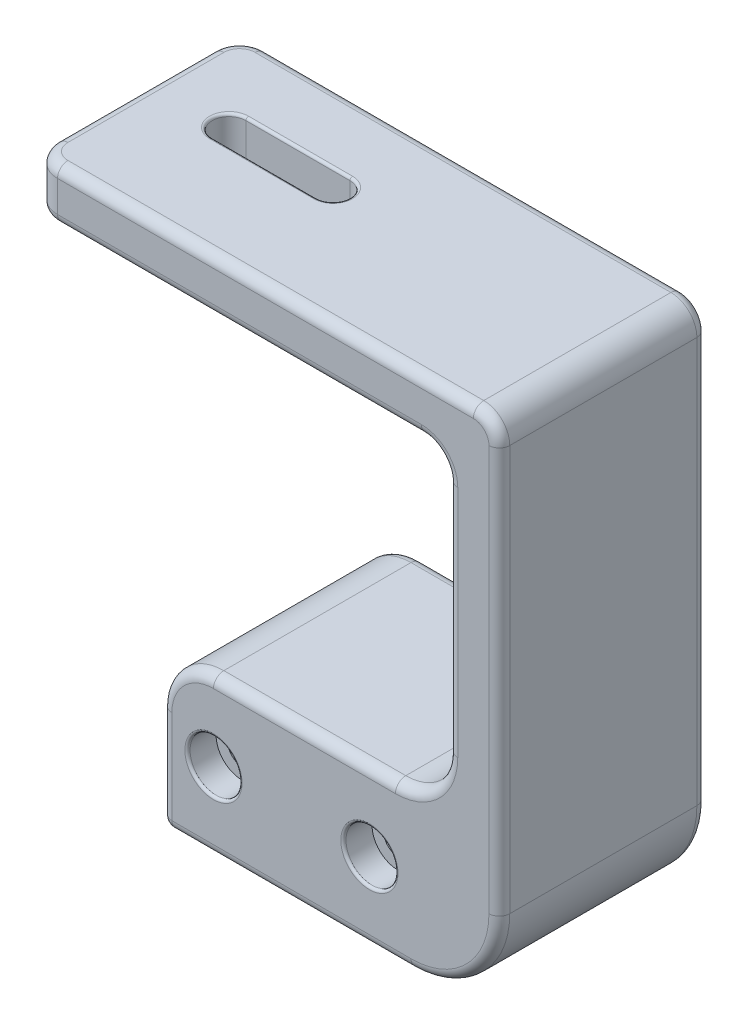
SolidWorks part; units mm, degrees
material "ABS"
ref_plane "Ebene vorne" through (0, 0, 0) normal (0, 0, 1) x (1, 0, 0)
ref_plane "Ebene oben" through (0, 0, 0) normal (0, 1, 0) x (1, 0, 0)
ref_plane "Ebene rechts" through (0, 0, 0) normal (1, 0, 0) x (0, 0, -1)
sketch "Skizze1" plane through (0, 0, 0) normal (0, 0, 1) x (1, 0, 0)
  line L0 (-50, 100) -> (-50, 90)
  line L1 (22, 0) -> (-22, 0) construction
  line L2 (30, 30) -> (-25, 30)
  line L3 (-50, 100) -> (40, 100)
  line L4 (40, 100) -> (40, 0)
  line L5 (40, 0) -> (-25, 0)
  line L6 (-50, 90) -> (30, 90)
  line L7 (-25, 0) -> (-25, 30)
  line L8 (0, -22) -> (0, 22) construction
  line L9 (30, 90) -> (30, 30)
  dimension "D2" = 55
  dimension "D1" = 25
  dimension "D3" = 10
  dimension "D5" = 100
  dimension "D4" = 65
  dimension "D6" = 30
  dimension "D7" = 90
extrude "Aufsatz-Linear austragen1" add sketch "Skizze1" along normal mid plane 40
sketch "Skizze3" plane through (0, 100, 0) normal (0, 1, 0) x (1, 0, 0)
  line L0 (-35, 3) -> (-15, 3) construction
  line L1 (-35, 6.25) -> (-15, 6.25)
  line L2 (-35, -0.25) -> (-15, -0.25)
  line L3 (-50, -20) -> (-50, 20) construction
  line L5 (40, 20) -> (-50, 20) construction
  arc A0 (-35, 6.25) -> (-35, -0.25) centre (-35, 3) ccw
  arc A1 (-15, -0.25) -> (-15, 6.25) centre (-15, 3) ccw
  point P3 (-25, 3)
  dimension "D1" = 6.5
  dimension "D2" = 20
  dimension "D3" = 15
  dimension "D4" = 17
extrude "Schnitt-Linear austragen1" cut sketch "Skizze3" against normal blind 20
sketch "Skizze5" plane through (0, 0, 20) normal (0, 0, 1) x (1, 0, 0)
  line L2 (0, -22) -> (0, 22) construction
  line L3 (-25, 0) -> (40, 0) construction
  point P0 (-15, 15)
  point P1 (15, 15)
  point P6 (3.3182, -18.595)
  point P7 (2.4434, -16.9467)
  dimension "D1" = 15
  dimension "D2" = 30
  dimension "D3" = 15
sketch "Skizze7" plane through (0, 0, 0) normal (0, -1, 0) x (1, 0, 0)
  line L0 (0, -22) -> (0, 22) construction
  line L1 (49.5, 0) -> (-49.5, 0) construction
  circle A0 centre (0, 10) radius 4
  circle A1 centre (0, -10) radius 4
  dimension "D1" = 8
  dimension "D2" = 20
  dimension "D3" = 10
extrude "Schnitt-Linear austragen3" cut sketch "Skizze7" against normal blind 12
hole_wizard "Stirnsenkung fur M3 Senkschraube (Kopf Button)1" positions "3D-Skizze1" profile "Skizze8" counterbore size "M3" standard "Ansi Metrisch" end condition through all
sketch3d "3D-Skizze1"
  point P0 (-15, 15, 20)
  point P3 (15, 15, 20)
sketch "Skizze8" plane through (-15, 15, 20) normal (1, 0, 0) x (0, -1, 0)
  line L0 (0, 0) -> (0, 40)
  line L1 (0, 40) -> (2.75, 40)
  line L3 (2.75, 40) -> (2.75, 5.5)
  line L4 (2.75, 5.5) -> (5, 5.5)
  line L5 (5, 5.5) -> (5, 0)
  line L7 (5, 0) -> (0, 0)
  line L11 (0, -6.35) -> (0, 107.95) construction
  dimension "Bohrerdurchmesser" = 5.5
  dimension "Bohrungstiefe" = 40
  dimension "Senkdurchmesser2" = 10
  dimension "Senktiefe2" = 5.5
fillet "Verrundung5" radius 17 1 edges at (40, 0, 0)
fillet "Verrundung6" radius 10 1 edges at (30, 30, 0)
fillet "Verrundung7" radius 10 1 edges at (-25, 30, 0)
fillet "Verrundung9" radius 5 4 edges at (40, 100, 0) (30, 90, 0) (-50, 95, 20) (-50, 95, -20)
fillet "Verrundung10" radius 2 31 edges at (-25, 10, -20) (-22.0711, 27.0711, -20) (2.5, 30, -20) (27.0711, 32.9289, -20) (30, 62.5, -20) (28.5355, 88.5355, -20) (-1, 0, -20) (35.0208, 4.9792, -20) (40, 56, -20) (38.5355, 98.5355, -20) (-1, 0, 20) (35.0208, 4.9792, 20) (40, 56, 20) (38.5355, 98.5355, 20) (-25, 10, 20) (-22.0711, 27.0711, 20) (2.5, 30, 20) (27.0711, 32.9289, 20) (30, 62.5, 20) (28.5355, 88.5355, 20) (-50, 100, 0) (-50, 90, 0) (-25, 0, 0) (-10, 90, -20) (-5, 100, -20) (-5, 100, 20) (-10, 90, 20) (-48.5355, 100, -18.5355) (-48.5355, 100, 18.5355) (-48.5355, 90, -18.5355) (-48.5355, 90, 18.5355)
fillet "Verrundung11" radius 0.5 10 edges at (-11.75, 100, -3) (-25, 100, 0.25) (-38.25, 100, -3) (-11.75, 90, -3) (-25, 90, 0.25) (-38.25, 90, -3) (-25, 100, -6.25) (-25, 90, -6.25) (20, 15, 20) (-10, 15, 20)
